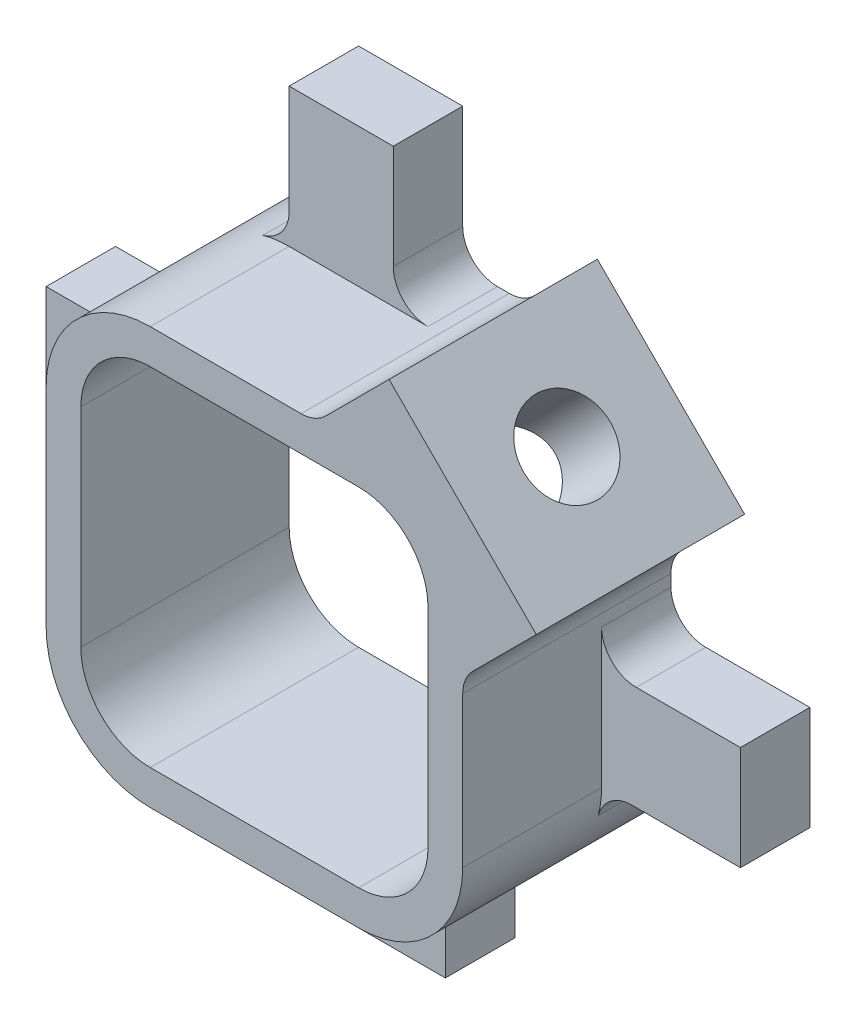
SolidWorks part; units mm, degrees
ref_plane "Ebene vorne" through (0, 0, 0) normal (0, 0, 1) x (1, 0, 0)
ref_plane "Ebene oben" through (0, 0, 0) normal (0, 1, 0) x (1, 0, 0)
ref_plane "Ebene rechts" through (0, 0, 0) normal (1, 0, 0) x (0, 0, -1)
sketch "Skizze1" plane through (0, 0, 0) normal (0, 0, 1) x (1, 0, 0)
  line L0 (0, 0) -> (6.7757, 6.7757) construction
  line L1 (-3, 3) -> (3, 3)
  line L2 (-3, 3) -> (-3, -3)
  line L3 (-3, -3) -> (3, -3)
  line L4 (3, 3) -> (3, -3)
  line L5 (-3, 3) -> (3, -3) construction
  line L6 (-3, -3) -> (3, 3) construction
  line L7 (1.9393, 4.0607) -> (4.0607, 1.9393)
  line L8 (1.9393, 4.0607) -> (0.8787, 3)
  line L9 (4.0607, 1.9393) -> (3, 0.8787)
  line L10 (-2.5, 2.5) -> (2.5, 2.5)
  line L11 (-2.5, 2.5) -> (-2.5, -2.5)
  line L12 (-2.5, -2.5) -> (2.5, -2.5)
  line L13 (2.5, 2.5) -> (2.5, -2.5)
  line L14 (-2.5, 2.5) -> (2.5, -2.5) construction
  line L15 (-2.5, -2.5) -> (2.5, 2.5) construction
  point P0 (0, 0)
  point P10 (3, 3)
  dimension "D1" = 6
  dimension "D2" = 6
  dimension "D3" = 90
  dimension "D4" = 90
  dimension "D5" = 3
  dimension "D6" = 3
  dimension "D7" = 3
  dimension "D8" = 90
  dimension "D9" = 5
  dimension "D10" = 5
extrude "Aufsatz-Linear austragen1" add sketch "Skizze1" along normal blind 3 contours L4 L1 L2 L3 L10 L13 L12 L11 | L7 L8 L1 | L9 L7 L4
fillet "Verrundung1" radius 1 4 edges at (2.5, -2.5, 1.5) (-2.5, -2.5, 1.5) (-2.5, 2.5, 1.5) (2.5, 2.5, 1.5)
sketch "Skizze2" plane through (0, 0, 0) normal (0, 0, 1) x (1, 0, 0)
  line L0 (-1.5, 3) -> (0, 3)
  line L1 (-1.5, 3) -> (-1.5, 5)
  line L2 (-1.5, 5) -> (0, 5)
  line L3 (0, 3) -> (0, 5)
  line L4 (-0.75, -5) -> (0.75, -5)
  line L5 (-0.75, -5) -> (-0.75, -3)
  line L6 (-0.75, -3) -> (0.75, -3)
  line L7 (0.75, -5) -> (0.75, -3)
  line L8 (-0.75, -5) -> (0.75, -3) construction
  line L9 (-0.75, -3) -> (0.75, -5) construction
  line L10 (-5, 0.75) -> (-3, 0.75)
  line L11 (-5, 0.75) -> (-5, -0.75)
  line L12 (-5, -0.75) -> (-3, -0.75)
  line L13 (-3, 0.75) -> (-3, -0.75)
  line L14 (-5, 0.75) -> (-3, -0.75) construction
  line L15 (-5, -0.75) -> (-3, 0.75) construction
  line L16 (3, 0) -> (5, 0)
  line L17 (3, 0) -> (3, -1.5)
  line L18 (3, -1.5) -> (5, -1.5)
  line L19 (5, 0) -> (5, -1.5)
  line L20 (-11.2678, 0) -> (11.2678, 0) construction
  line L21 (0, -7.7277) -> (0, 7.7277) construction
  point P4 (0, -4)
  point P9 (-4, 0)
  point P20 (0, 0)
  point P23 (0, 0)
  dimension "D1" = 1.5
  dimension "D2" = 1.5
  dimension "D3" = 1.5
  dimension "D4" = 1.5
  dimension "D5" = 5
  dimension "D6" = 5
  dimension "D7" = 5
  dimension "D8" = 5
extrude "Aufsatz-Linear austragen2" add sketch "Skizze2" along normal blind 1
fillet "Verrundung2" radius 1.5 3 edges at (3, -3, 1.5) (-3, -3, 1.5) (-3, 3, 1.5)
fillet "Verrundung3" radius 0.5 10 edges at (0, 3, 0.5) (0.8787, 3, 1.5) (3, 0.8787, 1.5) (3, 0, 0.5) (3, -1.5, 0.5) (0.75, -3, 0.5) (-0.75, -3, 0.5) (-3, -0.75, 0.5) (-3, 0.75, 0.5) (-1.5, 3, 0.5)
ref_plane "Ebene1" through (3, 3, 0) normal (0.7071, 0.7071, 0) x (0.7071, -0.7071, 0)
hole_wizard "M1.6 Gewindebohrung5" positions "Skizze3" profile "Skizze4" tap size "M1.6" standard "DIN"
sketch "Skizze3" plane through (3, 3, 0) normal (0.7071, 0.7071, 0) x (0.7071, -0.7071, 0)
  line L0 (-1.5, 0) -> (1.5, 0) construction
  line L1 (-1.5, -3) -> (-1.5, 0) construction
  point P0 (0, -1.5)
  dimension "D1" = 1.5
  dimension "D2" = 1.5
sketch "Skizze4" plane through (3, 3, 1.5) normal (0, 0, 1) x (-0.7071, 0.7071, 0)
  line L0 (0, 0) -> (0, 3.715)
  line L1 (0, 3.715) -> (0.625, 3.09)
  line L2 (0.625, 3.09) -> (0.625, 0)
  line L5 (0.625, 0) -> (0, 0)
  line L10 (0, 3.715) -> (-0.625, 3.09) construction
  line L11 (0, -6.35) -> (0, 107.95) construction
  dimension "Bohrerdurchmesser" = 1.25
  dimension "Bohrungstiefe" = 3.09
  dimension "Spitzenwinkel" = 90
cosmetic thread "Bohrungsgewinde3" parameters "D1"=1.34, "D2"=1.6
